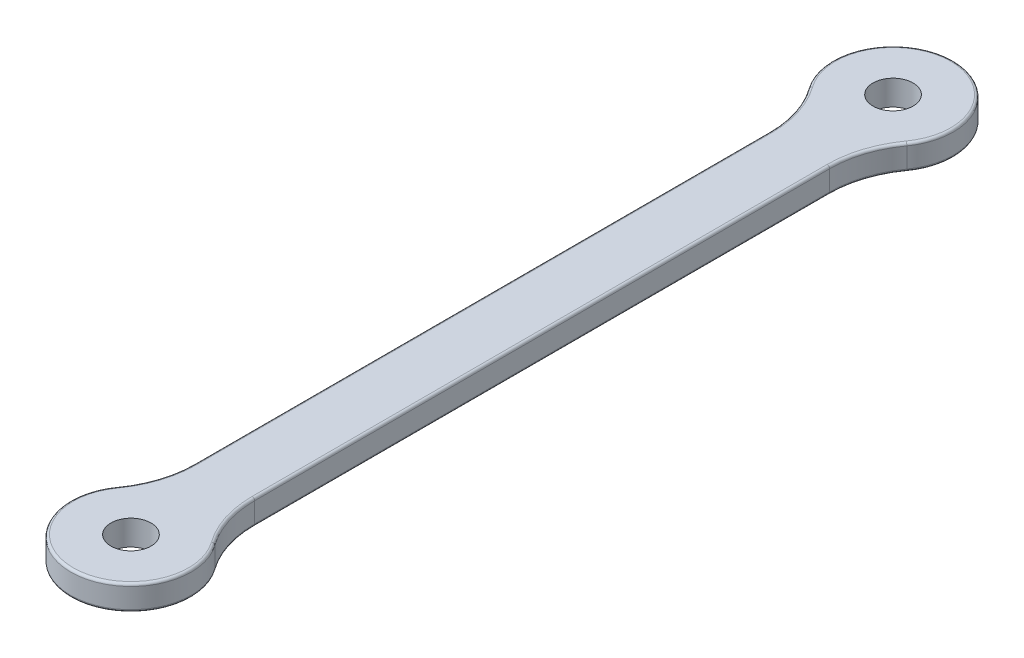
SolidWorks part; units mm, degrees
ref_plane "Front Plane" through (0, 0, 0) normal (0, 0, 1) x (1, 0, 0)
ref_plane "Top Plane" through (0, 0, 0) normal (0, 1, 0) x (1, 0, 0)
ref_plane "Right Plane" through (0, 0, 0) normal (1, 0, 0) x (0, 0, -1)
sketch "Sketch1" plane through (0, 0, 0) normal (0, 1, 0) x (1, 0, 0)
  line L1 (-3, -38) -> (3, -38)
  line L2 (-3, -38) -> (-3, 38)
  line L3 (-3, 38) -> (3, 38)
  line L4 (3, -38) -> (3, 38)
  line L5 (0, 38) -> (0, -38) construction
  line L6 (-3, 0) -> (3, 0) construction
  circle A0 centre (0, 38) radius 6
  circle A1 centre (0, 38) radius 2
  circle A2 centre (0, -38) radius 2
  circle A3 centre (0, -38) radius 6
  point P0 (0, 0)
  dimension "D2" = 12
  dimension "D5" = 4
  dimension "D3" = 76
  dimension "D4" = 6
extrude "Boss-Extrude1" add sketch "Sketch1" along normal blind 2.5 contours A3 L4 A0 L2 | A1 L4 A0 L2 | L2 A3 L4 A2 | L4 A3 L2 A2 | A1 L2 A0 L4
fillet "Fillet1" radius 10 4 edges at (-3, 1.25, 32.8038) (-3, 1.25, -32.8038) (3, 1.25, -32.8038) (3, 1.25, 32.8038)
fillet "Fillet2" radius 0.25 16 edges at (3.4803, 2.5, 31.7345) (3.4803, 0, 31.7345) (0, 2.5, 44) (0, 0, 44) (-3.4803, 2.5, 31.7345) (-3.4803, 0, 31.7345) (-3, 0, 0) (-3, 2.5, 0) (-3.4803, 2.5, -31.7345) (-3.4803, 0, -31.7345) (0, 0, -44) (0, 2.5, -44) (3.4803, 2.5, -31.7345) (3.4803, 0, -31.7345) (3, 0, 0) (3, 2.5, 0)
